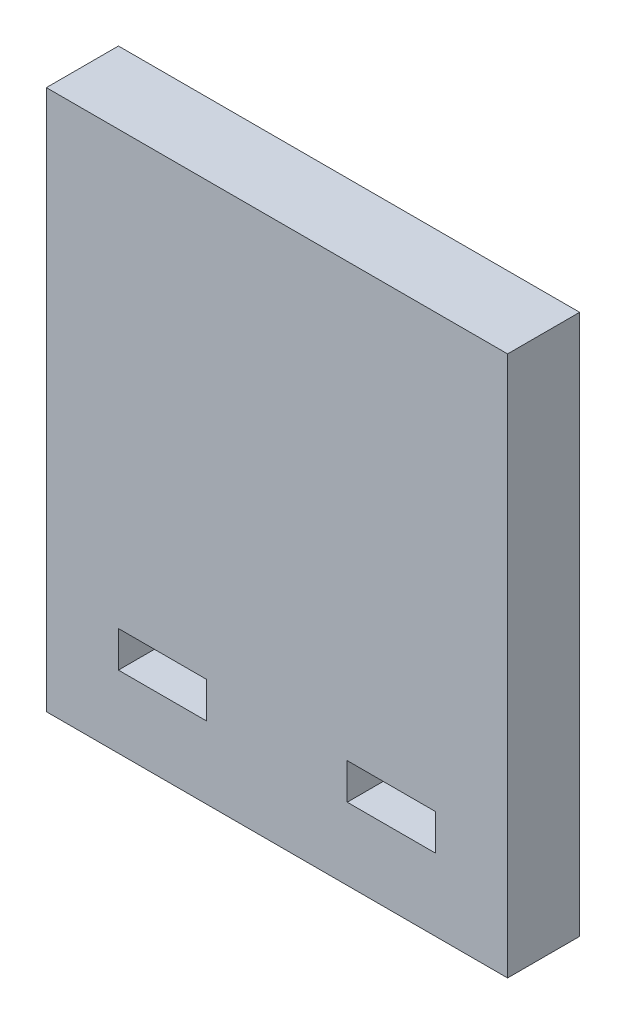
SolidWorks part; units mm, degrees
ref_plane "Front Plane" through (0, 0, 0) normal (0, 0, 1) x (1, 0, 0)
ref_plane "Top Plane" through (0, 0, 0) normal (0, 1, 0) x (1, 0, 0)
ref_plane "Right Plane" through (0, 0, 0) normal (1, 0, 0) x (0, 0, -1)
sketch "Sketch2" plane through (0, 0, 0) normal (0, 0, 1) x (1, 0, 0)
  line L0 (-972.7064, -55) -> (49027.2936, -55) construction
  line L1 (-64, -75) -> (64, -75)
  line L2 (-64, -75) -> (-64, 75)
  line L3 (-64, 75) -> (64, 75)
  line L4 (64, -75) -> (64, 75)
  line L5 (-64, -75) -> (64, 75) construction
  line L6 (-64, 75) -> (64, -75) construction
  line L7 (0, -1000) -> (0, 49000) construction
  line L8 (-44, -45) -> (-19.5, -45)
  line L9 (44, -55) -> (19.5, -55)
  line L10 (44, -55) -> (44, -45)
  line L11 (44, -45) -> (19.5, -45)
  line L12 (19.5, -55) -> (19.5, -45)
  line L13 (-19.5, -55) -> (-19.5, -45)
  line L14 (-44, -55) -> (-19.5, -55)
  line L15 (-44, -55) -> (-44, -45)
  point P0 (0, 0)
  dimension "D1" = 128
  dimension "D2" = 150
  dimension "D3" = 20
  dimension "D4" = 24.5
  dimension "D5" = 10
  dimension "D6" = 44
extrude "Boss-Extrude1" add sketch "Sketch2" along normal blind 20
